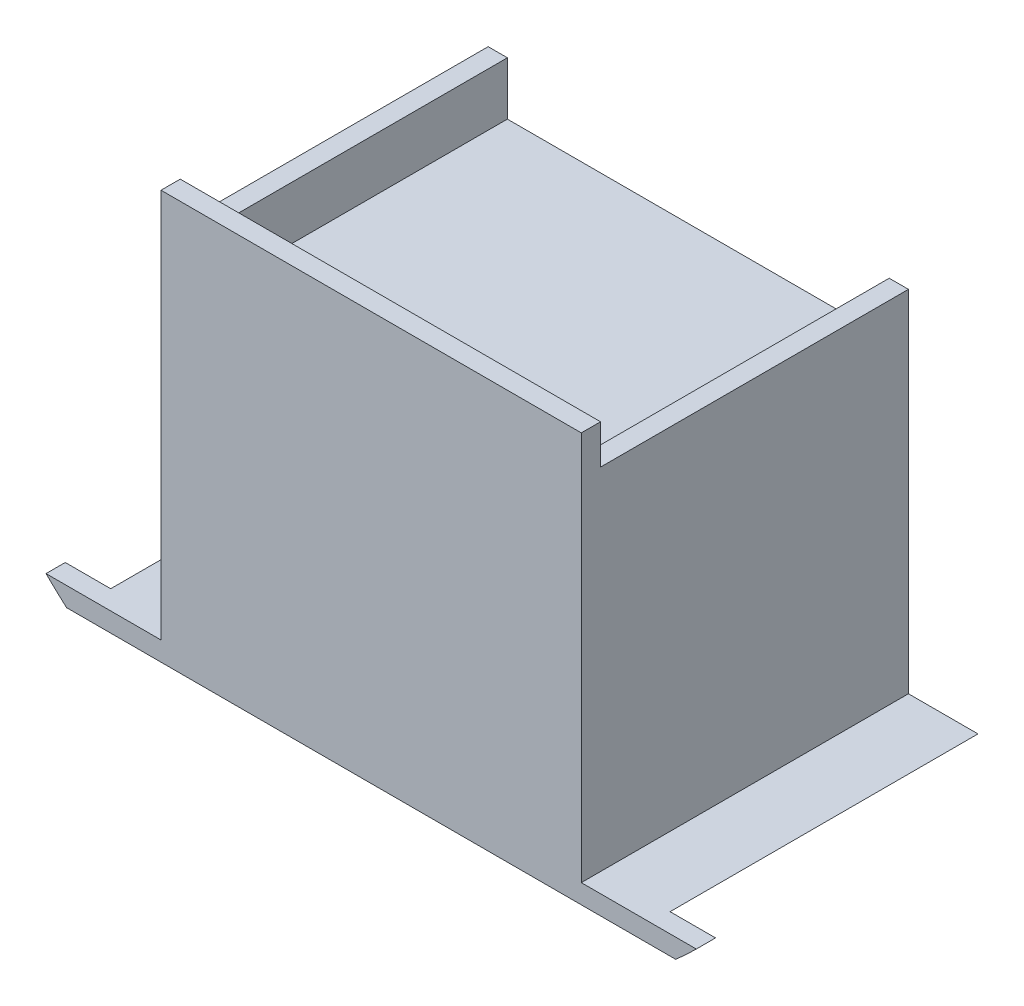
SolidWorks part; units mm, degrees
ref_plane "Front Plane" through (0, 0, 0) normal (0, 0, 1) x (1, 0, 0)
ref_plane "Top Plane" through (0, 0, 0) normal (0, 1, 0) x (1, 0, 0)
ref_plane "Right Plane" through (0, 0, 0) normal (1, 0, 0) x (0, 0, -1)
sketch "Sketch2" plane through (0, 0, 0) normal (0, 0, 1) x (1, 0, 0)
  line L0 (-34.671, -49.022) -> (-31.496, -49.022)
  line L1 (-31.496, -49.022) -> (-31.496, 0)
  line L2 (-31.496, 0) -> (31.496, 0)
  line L3 (31.496, 0) -> (31.496, -49.022)
  line L4 (31.496, -49.022) -> (34.671, -49.022)
  line L5 (34.671, -49.022) -> (34.671, 11.938)
  line L6 (34.671, 11.938) -> (31.496, 11.938)
  line L7 (31.496, 11.938) -> (31.496, 3.175)
  line L8 (31.496, 3.175) -> (-31.496, 3.175)
  line L9 (-31.496, 3.175) -> (-31.496, 11.938)
  line L10 (-31.496, 11.938) -> (-34.671, 11.938)
  line L11 (-34.671, 11.938) -> (-34.671, -49.022)
  line L12 (-31.496, 0) -> (-31.496, 3.175) construction
  point P13 (0, 0)
  dimension "D1" = 60.96
  dimension "D2" = 3.175
  dimension "D3" = 62.992
  dimension "D4" = 49.022
extrude "Boss-Extrude2" add sketch "Sketch2" along normal blind 50.8
sketch "Sketch3" plane through (0, 0, 50.8) normal (0, 0, 1) x (1, 0, 0)
  line L0 (34.671, -49.022) -> (34.671, 11.938) construction
  line L1 (-34.671, -49.022) -> (34.671, -49.022)
  line L2 (-34.671, -49.022) -> (-34.671, 18.415)
  line L3 (-34.671, 18.415) -> (34.671, 18.415)
  line L4 (34.671, -49.022) -> (34.671, 18.415)
  dimension "D1" = 67.437
extrude "Boss-Extrude3" add sketch "Sketch3" along normal blind 3.175
sketch "Sketch4" plane through (0, 0, 53.975) normal (0, 0, 1) x (1, 0, 0)
  line L0 (-34.671, -49.022) -> (-42.1386, -49.022)
  line L1 (-46.1453, -45.847) -> (-34.671, -45.847)
  line L2 (-34.671, 18.415) -> (-34.671, -49.022) construction
  line L3 (-34.671, -45.847) -> (-34.671, -49.022)
  line L4 (0, 0) -> (0, 8.2702) construction
  line L5 (34.671, -45.847) -> (34.671, -49.022)
  line L6 (46.1453, -45.847) -> (34.671, -45.847)
  line L7 (34.671, -49.022) -> (42.1386, -49.022)
  arc A0 (-42.1386, -49.022) -> (-46.1453, -45.847) centre (0, 8.2702) cw
  arc A1 (42.1386, -49.022) -> (46.1453, -45.847) centre (0, 8.2702) ccw
  dimension "D1" = 71.12
  dimension "D2" = 3.175
  dimension "D3" = 42.1386
extrude "Boss-Extrude4" add sketch "Sketch4" against normal up to surface (53.975 mm away) up to face at (0, -11.8322, 0)
sketch "Sketch5" plane through (0, 0, 53.975) normal (0, 0, -1) x (-1, 0, 0)
  line L0 (42.1386, -49.022) -> (50.2399, -49.022)
  line L1 (46.1453, -45.847) -> (53.6449, -45.847)
  line L2 (0, 0) -> (0, -49.022) construction
  line L3 (31.496, -49.022) -> (-31.496, -49.022) construction
  line L4 (-46.1453, -45.847) -> (-53.6449, -45.847)
  line L5 (-42.1386, -49.022) -> (-50.2399, -49.022)
  arc A0 (42.1386, -49.022) -> (46.1453, -45.847) centre (0, 8.2702) ccw construction
  arc A1 (42.1386, -49.022) -> (46.1453, -45.847) centre (0, 8.2702) ccw
  arc A2 (50.2399, -49.022) -> (53.6449, -45.847) centre (0, 8.2702) ccw
  arc A3 (-50.2399, -49.022) -> (-53.6449, -45.847) centre (0, 8.2702) cw
  arc A4 (-42.1386, -49.022) -> (-46.1453, -45.847) centre (0, 8.2702) cw
  dimension "D1" = 76.2
extrude "Boss-Extrude6" add sketch "Sketch5" along normal up to surface (3.175 mm away) up to face at (0, -24.511, 50.8)
sketch "Sketch6" plane through (0, 0, 50.8) normal (0, 0, -1) x (-1, 0, 0)
  line L4 (-31.496, -49.022) -> (31.496, -49.022)
  line L5 (31.496, -49.022) -> (31.496, 0)
  line L6 (31.496, 0) -> (-31.496, 0)
  line L7 (-31.496, 0) -> (-31.496, -49.022)
  line L8 (-31.496, -49.022) -> (31.496, -49.022)
  line L9 (31.496, -49.022) -> (31.496, 0)
  line L10 (31.496, 0) -> (-31.496, 0)
  line L11 (-31.496, 0) -> (-31.496, -49.022)
  dimension "D1" = 0
extrude "Boss-Extrude7" add sketch "Sketch6" along normal blind 25.4
